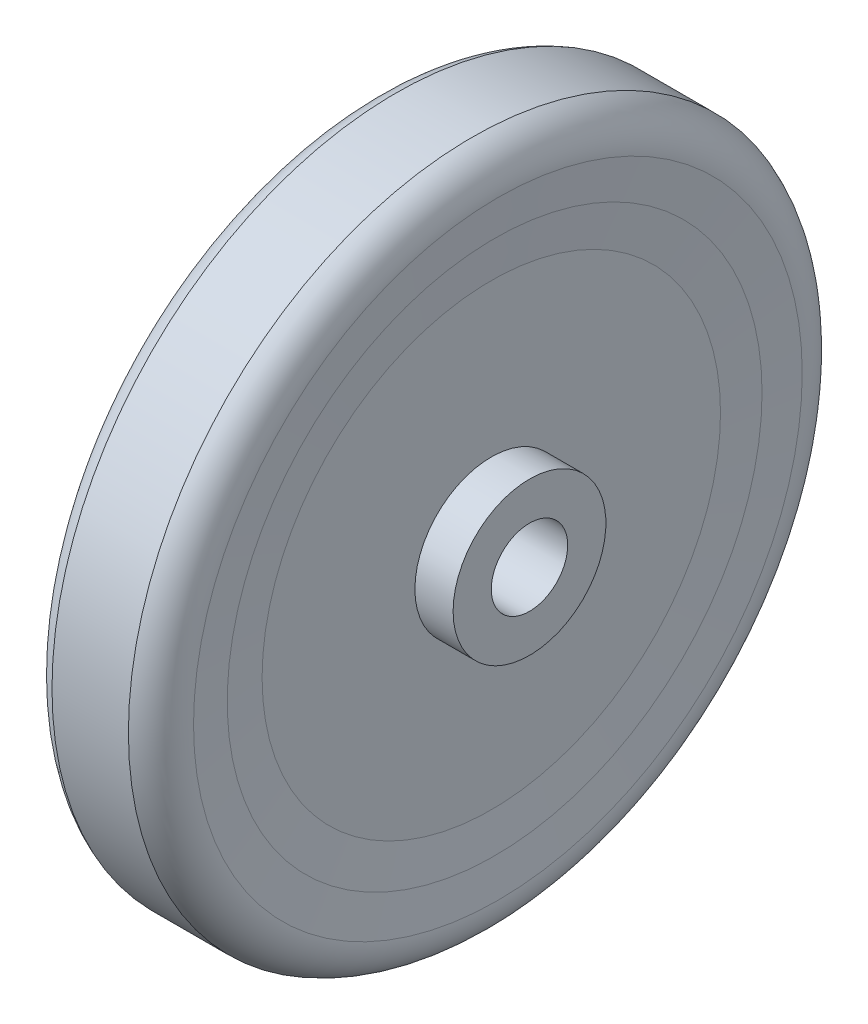
SolidWorks part; units mm, degrees
ref_plane "Ebene vorne" through (0, 0, 0) normal (0, 0, 1) x (1, 0, 0)
ref_plane "Ebene oben" through (0, 0, 0) normal (0, 1, 0) x (1, 0, 0)
ref_plane "Ebene rechts" through (0, 0, 0) normal (1, 0, 0) x (0, 0, -1)
sketch "Skizze1" plane through (0, 0, 0) normal (0, 0, 1) x (1, 0, 0)
  line L0 (0, 0) -> (12.5, 0) construction
  line L1 (-12.5, 5) -> (-12.5, 10)
  line L2 (-12.5, 10) -> (-7.5, 10)
  line L3 (-7.5, 10) -> (-7.5, 30)
  line L4 (-7.5, 30) -> (-8.3604, 39.8341)
  line L5 (7.5, 30) -> (7.5, 10)
  line L6 (7.5, 10) -> (12.5, 10)
  line L7 (12.5, 10) -> (12.5, 5)
  line L8 (12.5, 5) -> (-12.5, 5)
  line L9 (-5, 45) -> (5, 45)
  line L10 (7.5, 30) -> (8.3604, 39.8341)
  line L11 (0, 5) -> (0, 45) construction
  arc A0 (-8.3604, 39.8341) -> (-5, 45) centre (-3.3794, 40.2699) cw
  arc A1 (8.3604, 39.8341) -> (5, 45) centre (3.3794, 40.2699) ccw
  point P8 (0, 5)
  point P18 (0, 45)
  dimension "D9" = 5
  dimension "D1" = 10
  dimension "D2" = 20
  dimension "D3" = 60
  dimension "D4" = 25
  dimension "D5" = 15
  dimension "D6" = 90
  dimension "D7" = 10
  dimension "D8" = 10
revolve "Rotation1" add sketch "Skizze1" angle 360 about L0
sketch "Skizze2" plane through (0, 0, 0) normal (1, 0, 0) x (0, 0, -1)
  circle A0 centre (0, 0) radius 35
  dimension "D1" = 70
surface "Oberfläche-Linear austragen1" sketch "Skizze2" parameters "D1"=18
split "Abspalten1" trimming surface bodies 115 bodies to split 114 resulting bodies 116 117
delete or keep bodies "Körper-Löschen/beibehalten 1" type delete bodies bodies 115
